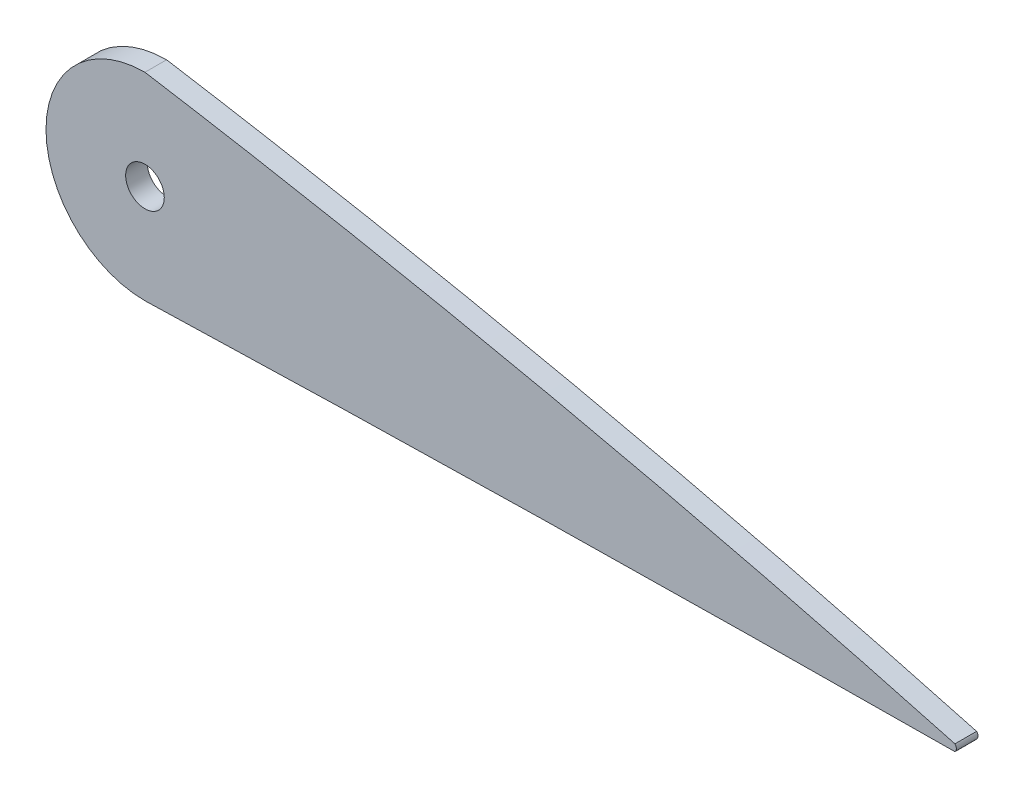
SolidWorks part; units mm, degrees
material "Фанера"
ref_plane "Front Plane" through (0, 0, 0) normal (0, 0, 1) x (1, 0, 0)
ref_plane "Top Plane" through (0, 0, 0) normal (0, 1, 0) x (1, 0, 0)
ref_plane "Right Plane" through (0, 0, 0) normal (1, 0, 0) x (0, 0, -1)
curve "Кривая1"
  spline degree 3 poles (0.0672, 0.87, 0) (0.0318, 0.5229, 0) (-0.0389, -0.1715, 0) (0.1092, -1.2382, 0) (0.4896, -2.2944, 0) (1.1401, -3.3111, 0) (2.0489, -4.255, 0) (3.2074, -5.1254, 0) (4.6283, -5.9301, 0) (6.3494, -6.6831, 0) (8.4416, -7.3951, 0) (11.0166, -8.0714, 0) (14.2364, -8.7104, 0) (18.3056, -9.2955, 0) (23.4194, -9.7901, 0) (29.6659, -10.1463, 0) (36.96, -10.3273, 0) (45.0764, -10.3268, 0) (53.7569, -10.166, 0) (62.8007, -9.8793, 0) (72.0812, -9.501, 0) (81.5234, -9.0613, 0) (91.0729, -8.586, 0) (100.6751, -8.0976, 0) (110.2799, -7.6156, 0) (119.8547, -7.1553, 0) (129.405, -6.7269, 0) (138.957, -6.3448, 0) (148.5363, -5.9896, 0) (158.1569, -5.6043, 0) (167.8102, -5.2124, 0) (177.4834, -4.8161, 0) (187.1542, -4.4222, 0) (196.8146, -4.0353, 0) (206.4608, -3.6595, 0) (216.0936, -3.2979, 0) (225.7151, -2.9531, 0) (235.3272, -2.6273, 0) (244.9322, -2.3221, 0) (254.532, -2.0389, 0) (264.1285, -1.7785, 0) (273.7233, -1.5416, 0) (283.3173, -1.3281, 0) (292.9097, -1.138, 0) (302.4935, -0.971, 0) (312.041, -0.8264, 0) (321.4647, -0.7041, 0) (330.5223, -0.6041, 0) (338.7731, -0.5271, 0) (345.1826, -0.4754, 0) (348.7687, -0.4498, 0) (350, -0.441, 0) knots 0 0 0 0 0.002941 0.005884 0.009016 0.012365 0.016008 0.020037 0.024574 0.029784 0.035897 0.04324 0.052276 0.063635 0.077983 0.095698 0.11652 0.139661 0.164312 0.189919 0.216157 0.242838 0.269834 0.296993 0.324123 0.351139 0.378036 0.404946 0.431961 0.459078 0.486347 0.513641 0.540929 0.568176 0.59538 0.622543 0.649673 0.676775 0.703855 0.730919 0.757971 0.785018 0.812062 0.839103 0.866132 0.893099 0.919831 0.94581 0.969681 0.98959 1 1 1 1
curve "Кривая2"
  spline degree 3 poles (350, 0.441, 0) (348.8179, 0.763, 0) (345.4082, 1.6919, 0) (339.3479, 3.3017, 0) (331.5897, 5.3027, 0) (323.0919, 7.4172, 0) (314.2383, 9.538, 0) (305.2428, 11.6083, 0) (296.1874, 13.6076, 0) (287.1014, 15.5293, 0) (277.9952, 17.371, 0) (268.8733, 19.1314, 0) (259.7387, 20.8097, 0) (250.5935, 22.4048, 0) (241.4399, 23.9153, 0) (232.28, 25.3398, 0) (223.1162, 26.6763, 0) (213.9505, 27.9228, 0) (204.7856, 29.077, 0) (195.6239, 30.1359, 0) (186.4686, 31.0968, 0) (177.3222, 31.956, 0) (168.1915, 32.7096, 0) (159.08, 33.3545, 0) (150.0138, 33.8803, 0) (141.0375, 34.2978, 0) (132.1765, 34.5613, 0) (123.4183, 34.6361, 0) (114.7287, 34.5224, 0) (106.0927, 34.2174, 0) (97.5152, 33.7146, 0) (89.0056, 33.0092, 0) (80.5773, 32.0949, 0) (72.2481, 30.9667, 0) (64.0422, 29.6192, 0) (55.9942, 28.0495, 0) (48.1571, 26.2588, 0) (40.6145, 24.2587, 0) (33.4961, 22.0806, 0) (26.979, 19.788, 0) (21.2507, 17.4767, 0) (16.4367, 15.2539, 0) (12.5431, 13.2014, 0) (9.4652, 11.352, 0) (7.0472, 9.6945, 0) (5.1404, 8.1959, 0) (3.6289, 6.8198, 0) (2.4334, 5.5336, 0) (1.4978, 4.3133, 0) (0.8003, 3.1383, 0) (0.3021, 2.0031, 0) (0.1432, 1.2365, 0) (0.0672, 0.87, 0) knots 0 0 0 0 0.010162 0.029313 0.052012 0.076619 0.101948 0.127526 0.153184 0.178868 0.204558 0.230246 0.255926 0.281594 0.307246 0.332878 0.358485 0.384061 0.409603 0.435104 0.460559 0.485959 0.511303 0.536552 0.561723 0.586629 0.611085 0.635251 0.659272 0.683164 0.706922 0.730536 0.753983 0.777235 0.800246 0.822951 0.845237 0.866916 0.887662 0.906968 0.924203 0.938879 0.950932 0.960693 0.968647 0.975233 0.980795 0.985584 0.989782 0.993521 0.996902 1 1 1 1
sketch "Эскиз2" plane through (0, 0, 0) normal (0, 0, 1) x (1, 0, 0)
  line L0 (350.1827, 0) -> (350.1827, 52.2565) construction
  line L39 (350.1827, 0) -> (433.3101, 0) construction
  arc A0 (350, 0.441) -> (350, -0.441) centre (349.559, 0) cw
  arc A9 (245.1827, 23.2937) -> (245.1827, -2.3181) centre (245.1827, 10.4878) ccw
  circle A11 centre (245.1827, 10.4878) radius 2.5
  spline S3 degree 3 poles (350, 0.441) (348.8179, 0.763) (345.4082, 1.6919) (339.3479, 3.3017) (331.5897, 5.3027) (323.0919, 7.4172) (314.2383, 9.538) (305.2428, 11.6083) (296.1874, 13.6076) (287.1014, 15.5293) (277.9952, 17.371) (268.8733, 19.1314) (259.7387, 20.8097) (251.8402, 22.1873) (246.9857, 22.9978) (245.1827, 23.2937) knots 0 0 0 0 0.010162 0.029313 0.052012 0.076619 0.101948 0.127526 0.153184 0.178868 0.204558 0.230246 0.255926 0.281594 0.29675 0.29675 0.29675 0.29675
  spline S6 degree 3 poles (245.1827, -2.3181) (248.2995, -2.2228) (254.6148, -2.0367) (264.1285, -1.7785) (273.7233, -1.5416) (283.3173, -1.3281) (292.9097, -1.138) (302.4935, -0.971) (312.041, -0.8264) (321.4647, -0.7041) (330.5223, -0.6041) (338.7731, -0.5271) (345.1826, -0.4754) (348.7687, -0.4498) (350, -0.441) knots 0.704556 0.704556 0.704556 0.704556 0.730919 0.757971 0.785018 0.812062 0.839103 0.866132 0.893099 0.919831 0.94581 0.969681 0.98959 1 1 1 1
  point P54 (245.1827, 23.2937)
  point P57 (245.1827, -2.3181)
  point P58 (245.1827, 23.2937)
  point P59 (245.1827, -2.3181)
  dimension "D1" = 0.6237
  dimension "D2" = 5
extrude "Бобышка-Вытянуть1" add sketch "Эскиз2" along normal mid plane 2.8
equation "\"Thickness\"= 2.8"
equation "\"chord\"= 350"
